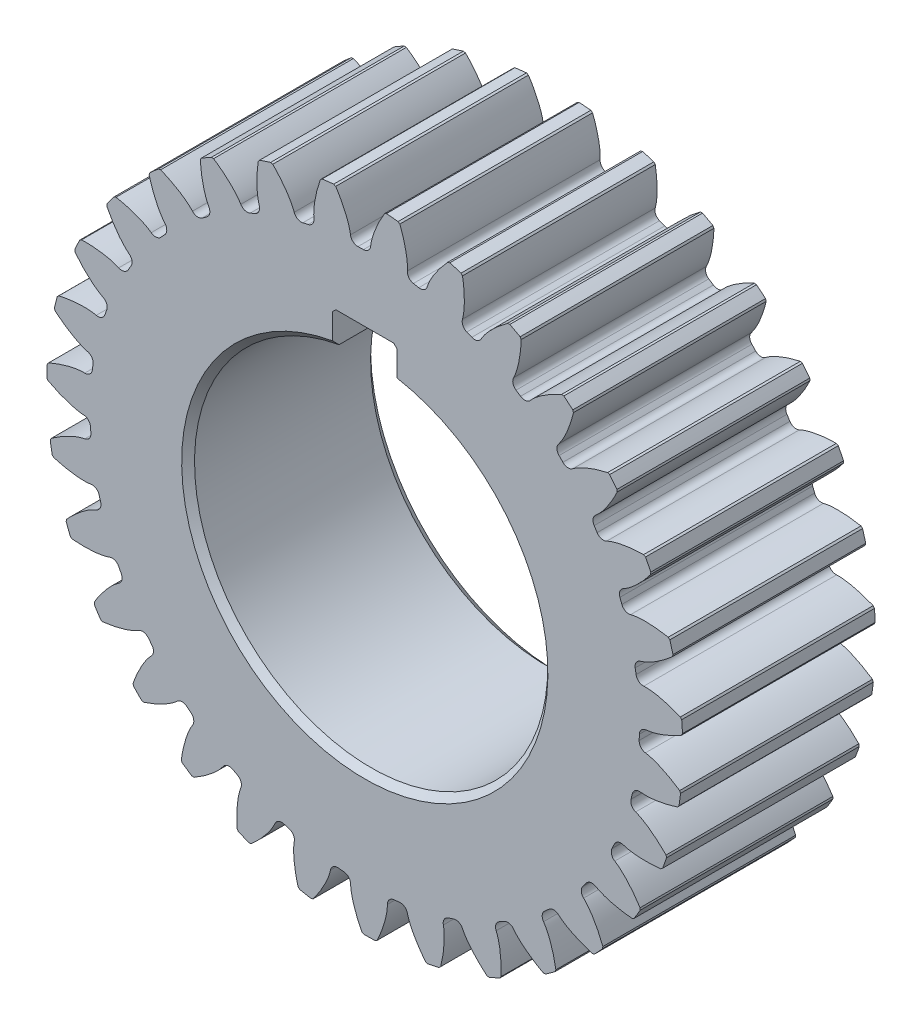
SolidWorks part; units mm, degrees
material "1.6587 (18CrNiMo7-6)"
ref_plane "Front Plane" through (0, 0, 0) normal (0, 0, 1) x (1, 0, 0)
ref_plane "Top Plane" through (0, 0, 0) normal (0, 1, 0) x (1, 0, 0)
ref_plane "Right Plane" through (0, 0, 0) normal (1, 0, 0) x (0, 0, -1)
sketch "Sketch1" plane through (0, 0, 0) normal (0, 0, 1) x (1, 0, 0)
  line L0 (0, 0) -> (0, 32.5) construction
  line L1 (5, 27.0416) -> (5, 32.5)
  line L2 (-5, 27.0416) -> (-5, 32.5)
  line L4 (5, 32.5) -> (-5, 32.5)
  line L5 (5, 0) -> (5, 32.5) construction
  line L6 (-5, 0) -> (-5, 32.5) construction
  arc A0 (-5, 27.0416) -> (5, 27.0416) centre (0, 0) ccw
  circle A1 centre (0, 0) radius 42.75
  dimension "D1" = 55
  dimension "D3" = 85.5
  dimension "D2" = 32.5
  dimension "D4" = 5
  dimension "D5" = 5
extrude "Boss-Extrude1" add sketch "Sketch1" along normal blind 30
sketch "Sketch2" plane through (0, 0, 0) normal (0, 0, 1) x (1, 0, 0)
  line L0 (0, 0) -> (46.4948, 0.693) construction
  line L1 (0, 0) -> (54.6331, 3.5877) construction
  arc A0 (42.7358, -1.1033) -> (42.2245, 6.6825) centre (0, 0) ccw
  circle A1 centre (0, 0) radius 46.5 construction
  arc A2 (49.4539, 2.135) -> (49.3084, 4.3507) centre (0, 0) ccw
  arc A3 (43.7974, 0.0046) -> (42.7358, -1.1033) centre (43.8754, -1.1327) ccw
  arc A4 (43.4219, 5.723) -> (42.2245, 6.6825) centre (43.3505, 6.8607) cw
  spline S0 degree 4 poles (43.6957, 0) (43.7055, 0.0001) (43.7329, 0.0008) (43.7847, 0.0034) (43.8692, 0.0098) (43.9767, 0.0207) (44.1156, 0.0382) (44.2791, 0.0631) (44.4584, 0.0949) (44.6533, 0.1344) (44.8473, 0.178) (45.0406, 0.2256) (45.2328, 0.2765) (45.4652, 0.3424) (45.7434, 0.4274) (46.0675, 0.5352) (46.4339, 0.6676) (46.806, 0.8133) (47.1708, 0.9655) (47.538, 1.1294) (47.8922, 1.2952) (48.2584, 1.4778) (48.5956, 1.6516) (48.9714, 1.8577) (49.2741, 2.0274) (49.6711, 2.2633) (49.9049, 2.4063) (50.1777, 2.5778) (50.2984, 2.6561) (50.3728, 2.7043) knots 0 0 0 0 0 0.005377 0.015084 0.028532 0.04661 0.064855 0.092111 0.119476 0.146842 0.174209 0.201575 0.228941 0.256307 0.307035 0.361767 0.4165 0.471232 0.525964 0.580697 0.635429 0.690161 0.744894 0.799626 0.854358 0.909091 0.954545 1 1 1 1 1 construction
  spline S1 degree 4 poles (43.7974, 0.0046) (43.8238, 0.0064) (43.8828, 0.0112) (43.9748, 0.0205) (44.1156, 0.0382) (44.2791, 0.0631) (44.4584, 0.0949) (44.6533, 0.1344) (44.8473, 0.178) (45.0406, 0.2256) (45.2328, 0.2765) (45.4652, 0.3424) (45.7434, 0.4274) (46.0675, 0.5352) (46.4339, 0.6676) (46.806, 0.8133) (47.1708, 0.9655) (47.538, 1.1294) (47.8922, 1.2952) (48.2584, 1.4778) (48.5956, 1.6516) (48.965, 1.8542) (49.1881, 1.9792) (49.3679, 2.0842) (49.4539, 2.135) knots 0.014009 0.014009 0.014009 0.014009 0.014009 0.028532 0.04661 0.064855 0.092111 0.119476 0.146842 0.174209 0.201575 0.228941 0.256307 0.307035 0.361767 0.4165 0.471232 0.525964 0.580697 0.635429 0.690161 0.744894 0.799626 0.850632 0.850632 0.850632 0.850632 0.850632
  spline S2 degree 4 poles (43.4219, 5.723) (43.4482, 5.7246) (43.5074, 5.7277) (43.5998, 5.7305) (43.7418, 5.7313) (43.907, 5.728) (44.089, 5.7199) (44.2874, 5.7063) (44.4855, 5.6884) (44.6833, 5.6665) (44.8805, 5.6412) (45.1196, 5.6062) (45.4064, 5.5584) (45.7419, 5.4938) (46.1225, 5.4105) (46.5104, 5.3147) (46.892, 5.2115) (47.2775, 5.097) (47.6503, 4.979) (48.0373, 4.8459) (48.3943, 4.7177) (48.787, 4.5651) (49.0245, 4.4704) (49.2165, 4.3898) (49.3084, 4.3507) knots 0.014009 0.014009 0.014009 0.014009 0.014009 0.028532 0.04661 0.064855 0.092111 0.119476 0.146842 0.174209 0.201575 0.228941 0.256307 0.307035 0.361767 0.4165 0.471232 0.525964 0.580697 0.635429 0.690161 0.744894 0.799626 0.850632 0.850632 0.850632 0.850632 0.850632
  dimension "D1" = 93
  dimension "D2" = 85.5
  dimension "D3" = 99
  dimension "D4" = 2.28
  dimension "D5" = 2.903
extrude "Boss-Extrude2" add sketch "Sketch2" along normal blind 30
chamfer "Chamfer1" distance 0.2 2 edges at (49.4539, 2.135, 15) (49.3084, 4.3507, 15)
pattern_circular "CirPattern1" count 31 over 360 about axis through (0, 0, 30) along (0, 0, -1) of "Chamfer1", "Boss-Extrude2"
chamfer "Chamfer2" distance 1.6 1 edges at (0, -27.5, 0)
chamfer "Chamfer3" distance 1 1 edges at (0, -27.5, 30)
chamfer "Chamfer4" distance 0.5 2 edges at (5, 32.5, 15) (-5, 32.5, 15)
